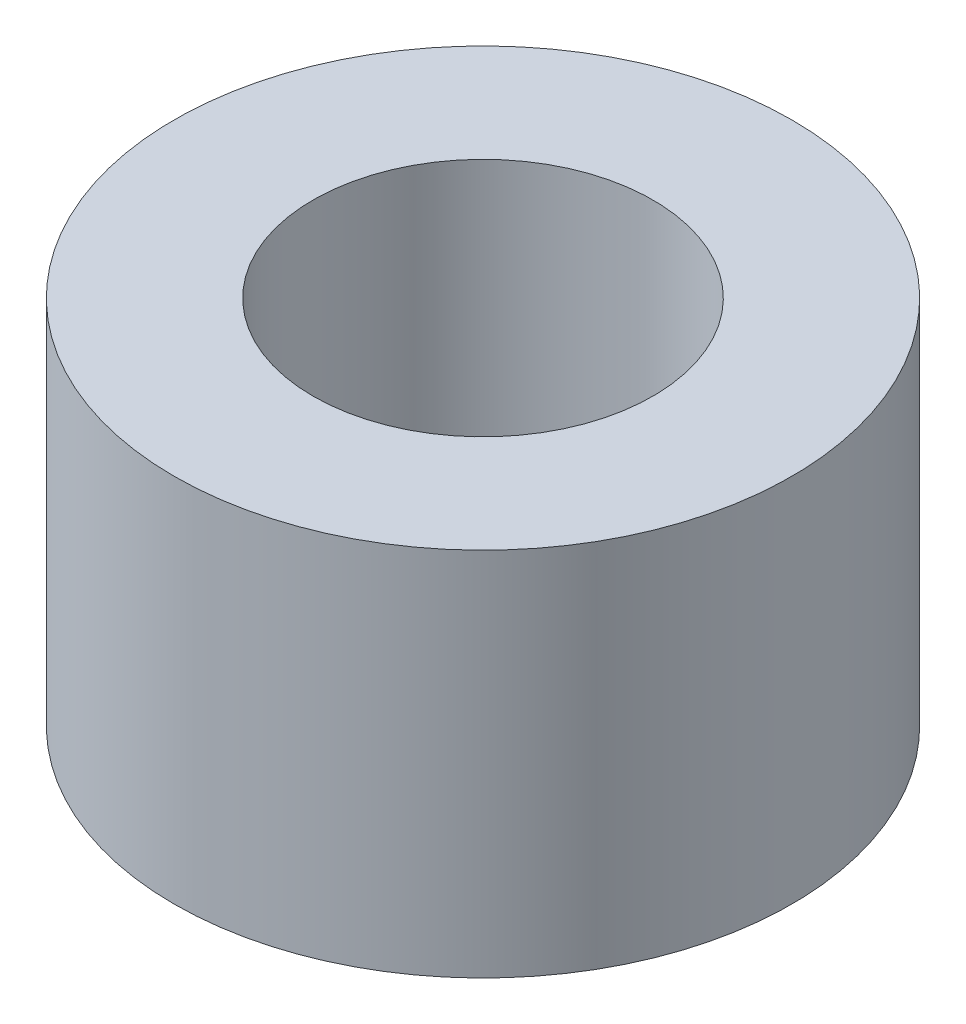
SolidWorks part; units mm, degrees
material "6061 Alloy"
ref_plane "Front Plane" through (0, 0, 0) normal (0, 0, 1) x (1, 0, 0)
ref_plane "Top Plane" through (0, 0, 0) normal (0, 1, 0) x (1, 0, 0)
ref_plane "Right Plane" through (0, 0, 0) normal (1, 0, 0) x (0, 0, -1)
sketch "Sketch1" plane through (0, 0, 0) normal (0, 1, 0) x (1, 0, 0)
  circle A0 centre (0, 0) radius 3.9688
  circle A1 centre (0, 0) radius 2.1844
  dimension "D1" = 4.3688
  dimension "D2" = 7.9375
extrude "Boss-Extrude1" add sketch "Sketch1" along normal blind 4.7625
